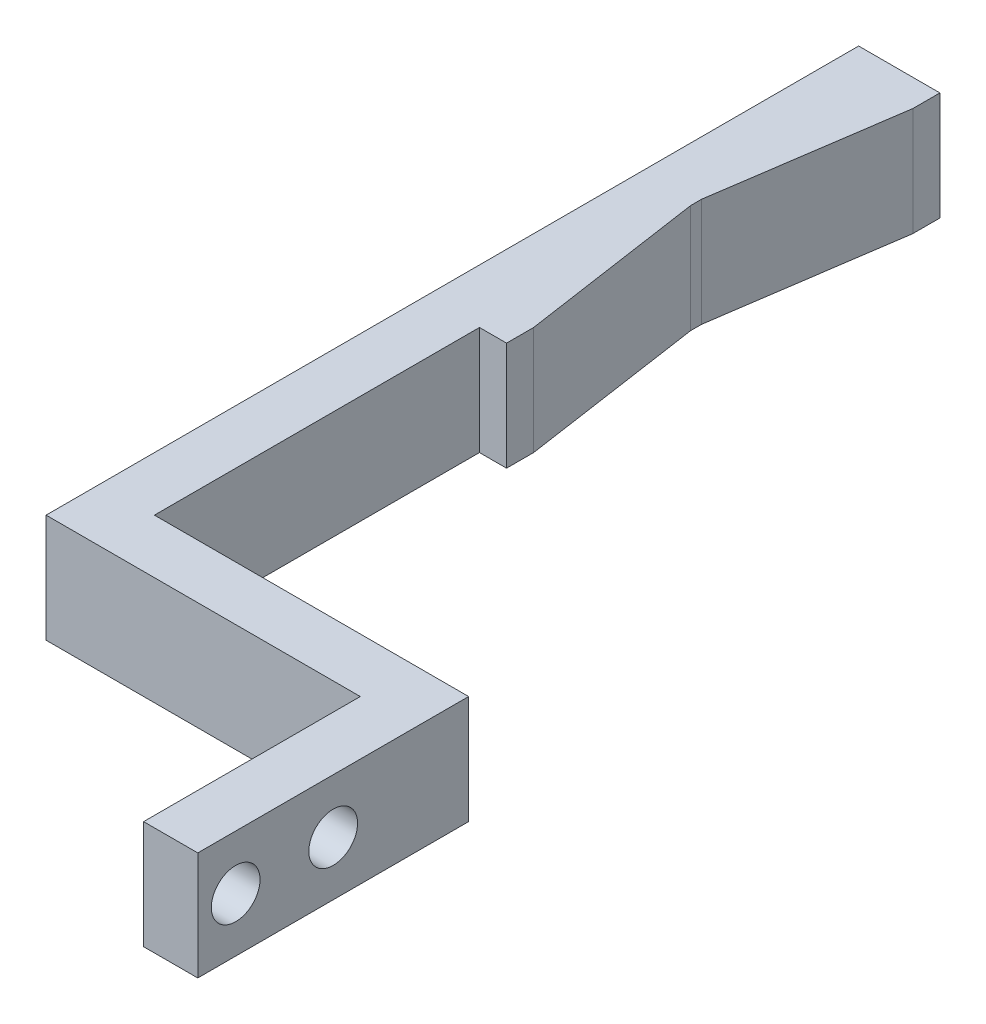
SolidWorks part; units mm, degrees
material "100MnCrW4"
ref_plane "Front Plane" through (0, 0, 0) normal (0, 0, 1) x (1, 0, 0)
ref_plane "Top Plane" through (0, 0, 0) normal (0, 1, 0) x (1, 0, 0)
ref_plane "Right Plane" through (0, 0, 0) normal (1, 0, 0) x (0, 0, -1)
sketch "Sketch2" plane through (0, 0, 0) normal (0, 1, 0) x (1, 0, 0)
  line L0 (0, 0) -> (0, 25)
  line L1 (0, 25) -> (-29, 25)
  line L2 (-29, 25) -> (-29, 95)
  line L3 (-29, 95) -> (-34, 95)
  line L4 (-34, 95) -> (-34, 20)
  line L5 (-34, 20) -> (-5, 20)
  line L6 (-5, 20) -> (-5, 0)
  line L7 (-5, 0) -> (0, 0)
  line L8 (-29, 95) -> (-26.5, 95)
  line L9 (-26.5, 95) -> (-26.5, 92.5)
  line L10 (-26.5, 92.5) -> (-29, 75.5)
  line L12 (-29, 74.5) -> (-26.5, 57.5)
  line L13 (-26.5, 57.5) -> (-26.5, 55)
  line L14 (-26.5, 55) -> (-29, 55)
  line L15 (-26.5, 92.5) -> (-26.5, 57.5) construction
  dimension "D7" = 1
  dimension "D6" = 29
  dimension "D1" = 25
  dimension "D2" = 5
  dimension "D3" = 70
  dimension "D4" = 5
  dimension "D5" = 5
  dimension "D8" = 2.5
  dimension "D9" = 40
  dimension "D11" = 2.5
extrude "Boss-Extrude1" add sketch "Sketch2" along normal blind 10 contours L6 L7 L0 L1 L2 L3 L4 L5 | L14 L13 L12 L2 | L10 L9 L8 L2
sketch "Sketch3" plane through (0, 0, 0) normal (1, 0, 0) x (0, 0, -1)
  line L0 (0, 10) -> (0, 0) construction
  circle A0 centre (3.5, 5) radius 2.25
  circle A1 centre (12.5, 5) radius 2.25
  point P8 (0, 5)
  dimension "D1" = 4.5
  dimension "D2" = 9
  dimension "D3" = 3.5
extrude "Cut-Extrude1" cut sketch "Sketch3" against normal through all
